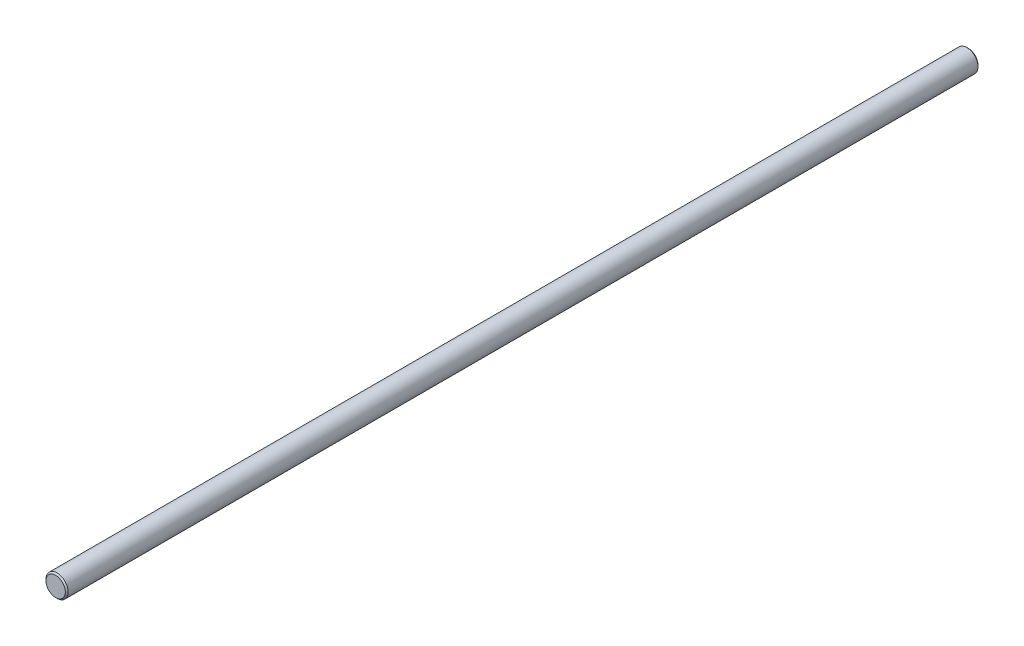
SolidWorks part; units mm, degrees
material "AISI 304"
ref_plane "Front Plane" through (0, 0, 0) normal (0, 0, 1) x (1, 0, 0)
ref_plane "Top Plane" through (0, 0, 0) normal (0, 1, 0) x (1, 0, 0)
ref_plane "Right Plane" through (0, 0, 0) normal (1, 0, 0) x (0, 0, -1)
sketch "Sketch1" plane through (0, 0, 0) normal (0, 0, 1) x (1, 0, 0)
  circle A0 centre (0, 0) radius 4
  dimension "D1" = 8
extrude "Boss-Extrude1" add sketch "Sketch1" against normal blind 330
cosmetic thread "Cosmetic Thread1" parameters "D2"=6.619
chamfer "Chamfer1" distance 0.5 angle 45 2 edges at (4, 0, -330) (4, 0, 0)
